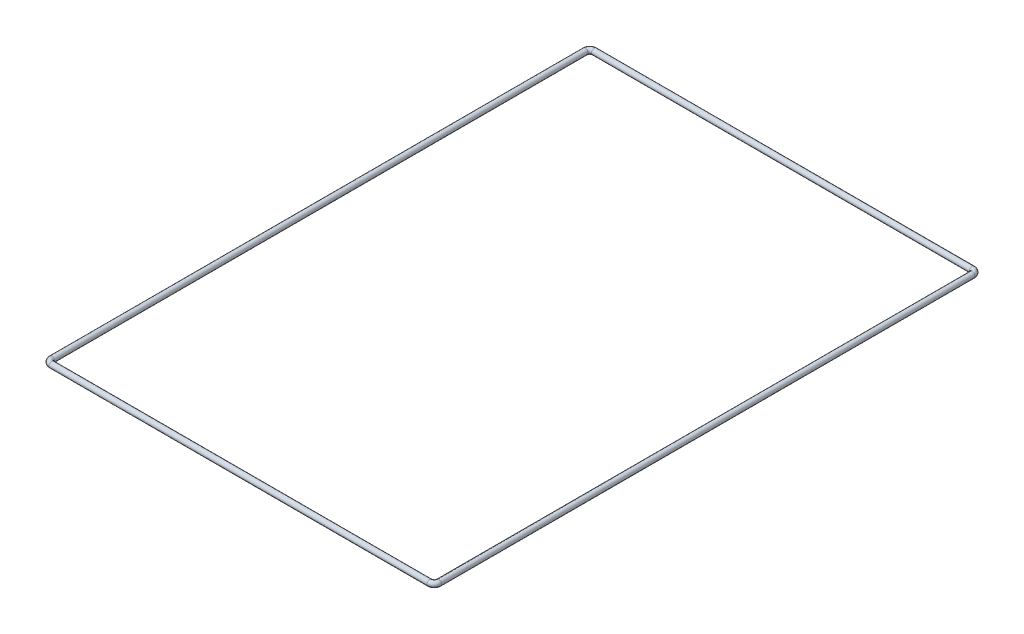
SolidWorks part; units mm, degrees
ref_plane "Front Plane" through (0, 0, 0) normal (0, 0, 1) x (1, 0, 0)
ref_plane "Top Plane" through (0, 0, 0) normal (0, 1, 0) x (1, 0, 0)
ref_plane "Right Plane" through (0, 0, 0) normal (1, 0, 0) x (0, 0, -1)
sketch3d "3DSketch1"
  line L0 (0, 0, 591.7622) -> (0, 0, -159.2269)
  line L1 (6.35, 0, -165.5769) -> (538.3657, 0, -165.5769)
  line L2 (544.7157, 0, -159.2269) -> (544.7157, 0, 591.7622)
  line L3 (538.3657, 0, 598.1122) -> (6.35, 0, 598.1122)
  arc A0 (538.3657, 0, -165.5769) -> (544.7157, 0, -159.2269) centre (538.3657, 0, -159.2269) ccw
  arc A1 (0, 0, -159.2269) -> (6.35, 0, -165.5769) centre (6.35, 0, -159.2269) ccw
  arc A2 (0, 0, 591.7622) -> (6.35, 0, 598.1122) centre (6.35, 0, 591.7622) ccw
  arc A3 (544.7157, 0, 591.7622) -> (538.3657, 0, 598.1122) centre (538.3657, 0, 591.7622) ccw
  point P7 (544.7157, 0, -165.5769)
  point P8 (538.3657, -6.35, -159.2269)
  point P11 (0, 0, -165.5769)
  point P12 (6.35, -6.35, -159.2269)
  point P15 (0, 0, 0)
  point P16 (6.35, 6.35, 591.7622)
  point P19 (544.7157, 0, 598.1122)
  point P20 (538.3657, -6.35, 591.7622)
  dimension "D2" = 544.7157
  dimension "D1" = 6.35
  dimension "D3" = 763.6891
ref_plane "Plane1" through (0, 0, 591.7622) normal (0, 0, -1) x (-1, 0, 0)
sketch "Sketch2" plane through (0, 0, 591.7622) normal (0, 0, -1) x (-1, 0, 0)
  circle A0 centre (0, 0) radius 3.9688
  circle A1 centre (0, 0) radius 2.3813
  dimension "D1" = 7.9375
  dimension "D2" = 4.7625
sweep "Sweep1" add profiles "Sketch2" path "3DSketch1"
equation "\"Height\"= 32in"
equation "\"Width\"= 23in"
equation "\"Depth\"= 20in"
equation "\"Plexi\"= .121in"
equation "\"EBWidth\" = 9in"
equation "\"ComponentMountDia\"=0.1770"
equation "\"MagnetThickness\"= .125in"
equation "\"MagnetDiameter\"= 12mm"
equation "\"DoorPlexi\" = \"Plexi\""
equation "\"ShelfThickness\" = .1250in"
equation "\"BasePlateThickness\" = 0.5in"
equation "\"BasePlateWidth\" = \"Width\"+\"EBWidth\"-2*\"Plexi\""
equation "\"BasePlateDepth\" = \"TopBarDepth\"+2*\"CornerCube\""
equation "\"Boxsize\" = .75in"
equation "\"BoxsizeHalf\" = \"Boxsize\"/2"
equation "\"Boxinner\" = .625in"
equation "\"CornerCube\" = 0.75in"
equation "\"FingerLength\" = 1.125in"
equation "\"FingerWidth\" = .625in"
equation "\"Cutwidth\"= .016in"
equation "\"Earsize\"= 1in + \"Cutwidth\" /2"
equation "\"Slotsize\" = 1in - \"CutWidth\" / 2"
equation "\"InnerWidth\" = \"Width\" - 2* \"Plexi\""
equation "\"InnerHeight\" = \"Height\" -2 * \"Plexi\""
equation "\"InnerDepth\" = \"Depth\" - 2*\"Plexi\""
equation "\"FrontDoorGap\" = .1in"
equation "\"TopDepth\" = \"Depth\"-\"DoorPlexi\"-\"FrontDoorGap\""
equation "\"TopBarDepth\" = \"Depth\"-\"DoorPlexi\"-\"Plexi\"-2*\"MagnetThickness\"-2*\"CornerCube\""
equation "\"RearNumHoles\" = 4"
equation "\"RearHolesBorder\" = 2.25"
equation "\"RearHoleSpacing\" = (\"Width\" - 2*\"RearHolesBorder\") / (\"RearNumHoles\"-1)"
equation "\"RearBarLength\" = (\"InnerWidth\"-2*\"CornerCube\")"
equation "\"RearTopNumHoles\" = 4"
equation "\"RearTopHolesBorder\" = 3.1"
equation "\"RearTopHolesSpacing\" = (\"Width\" - 2*\"RearTopHolesBorder\") / (\"RearTopNumHoles\"-1)"
equation "\"SideTopNumHoles\" = 4"
equation "\"SideTopHoleOffset\"=\"CornerCube\"+\"FingerLength\"+\"Plexi\"+.5"
equation "\"SideTopHoleSpacing\" = (\"TopBarDepth\"-2*\"SideTopHoleOffset\") / (\"SideTopNumHoles\"-1)"
equation "\"SideHorizNumHoles\" = 4"
equation "\"SideHorizHoleBorder\" = 1.50"
equation "\"SideHorizHoleSpacing\" = (\"TopBarDepth\"-2*\"SideHorizHoleBorder\") / (\"SideHorizNumHoles\"-1)"
equation "\"SideVertBarLength\"=\"Height\"-\"BasePlateThickness\"-2*\"CornerCube\"-\"Plexi\""
equation "\"SideVertNumHoles\" = 4"
equation "\"SideVertHolesBorder\" = \"CornerCube\"+\"FingerLength\"+1.50"
equation "\"SideVertHoleSpacing\" = (\"InnerHeight\" - 2*\"SideVertHolesBorder\") / (\"SideVertNumHoles\"-1)"
equation "\"RearSideVertNumHoles\" = 4"
equation "\"RearSideVertHolesBorder\" = 2.4"
equation "\"RearSideVertHoleSpacing\" = (\"InnerHeight\" - 2*\"RearSideVertHolesBorder\") / (\"RearSideVertNumHoles\"-1)"
equation "\"Rivet3_16Dia\" = .191in"
equation "\"RivetDia\" = .228in"
equation "\"BinderPostDia\" = .228in"
equation "\"SlotDepth\" = \"Plexi\" + 0.75in + .005in"
equation "\"SideSlotWidth\"   = \"Plexi\"+.005in"
equation "\"SidePanelVertSpacing\" = (\"Height\"-2*(1.75-\"Plexi\")) / 5"
equation "\"BottomPanelSideHoleSpacing\" = (\"InnerDepth\"-2*(1.75-\"Plexi\")) / 4"
equation "\"CoolerDepth\" = 12in"
equation "\"ShelfGap\" = 0.5in"
equation "\"ShelfDepth\" = \"TopBarDepth\"+\"CornerCube\"-\"CoolerDepth\""
equation "\"ShelfBarDepth\"=\"ShelfDepth\"-2*\"CornerCube\""
equation "\"ShelfWidth\" = \"EBWidth\"-\"ShelfGap\""
equation "\"ShelfBarWidth\" = \"EBWidth\"-\"Boxsize\""
equation "\"ShelfBarWidthShort\" = \"ShelfBarWidth\"-\"Boxsize\"-\"ShelfGap\""
equation "\"ShelfHeight1\" = 13in"
equation "\"ShelfHeight2\" = 24in"
equation "\"IntakeWidth\"=4in"
equation "\"IntakeHeight\"=2in"
equation "\"ExhaustWidth\"=4in"
equation "\"ExhaustHeight\"=2in"
equation "\"VentSpacing\"=7in"
equation "\"VentVertLocation\"=12.75in"
equation "\"AngleBracketLengthShort\"=.625in"
equation "\"AngleBracketLengthLong\"=1in"
equation "\"AngleBracketWidth\"=.5in"
equation "\"AngleBracketThickness\"=.125in"
equation "\"AngleBracketHolePosShort\"=.3125in"
equation "\"AngleBracketHolePosLong\"=.640625in"
equation "\"AngleBracketHoleDia\"=\"Rivet3_16Dia\""
equation "\"ShelfBarAngleHole\"=\"ShelfGap\"+\"Boxsize\"+\"AngleBracketHolePosShort\""
equation "\"PSBracketThickness\" = .0641in"
equation "\"EBForwardMountOffset\" = 4.0in"
equation "\"EBForwardMount\" = 2*\"Boxsize\"+\"CoolerDepth\"+\"EBForwardMountOffset\""
equation "\"EBRearwardMountOffset\" = 1.5in"
equation "\"EBRearwardMount\"= \"Boxsize\"+\"EBRearwardMountOffset\""
equation "\"MagSealWidth\" = \"InnerWidth\""
equation "\"MagSealHeight\" = \"Height\"-\"BasePlateThickness\"-\"Plexi\""
equation "\"MagWidth\" = .500in"
equation "\"SiliconeSealOD\" = .3125in"
equation "\"SiliconeSealID\" = .1875in"
equation "\"SiliconeSealWidth\" = \"MagSealWidth\" - 2*\"MagWidth\"-\"SiliconeSealOD\""
equation "\"SiliconeSealHeigth\" = \"MagSealHeight\" - 2*\"MagWidth\"-\"SiliconeSealOD\""
equation "\"D1@Sketch2\"=\"SiliconeSealOD\""
equation "\"D2@3DSketch1\"=\"SiliconeSealWidth\""
equation "\"D3@3DSketch1\"=\"SiliconeSealHeigth\""
equation "\"D2@Sketch2\"=\"SiliconeSealID\""
